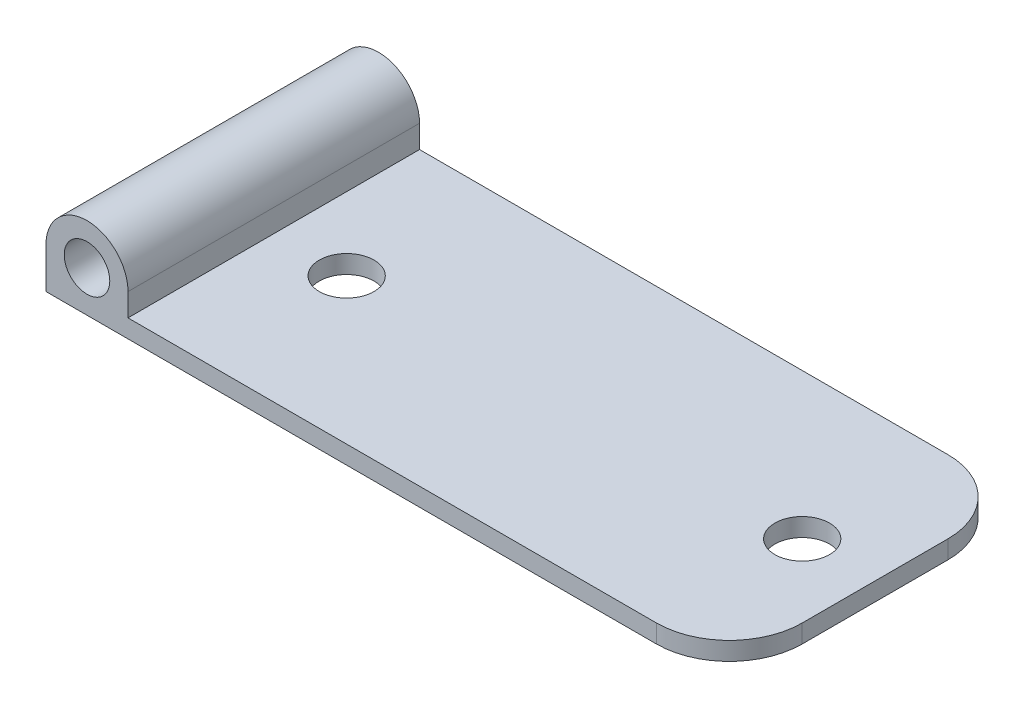
SolidWorks part; units mm, degrees
material "6061-T6 (SS)"
ref_plane "Front Plane" through (0, 0, 0) normal (0, 0, 1) x (1, 0, 0)
ref_plane "Top Plane" through (0, 0, 0) normal (0, 1, 0) x (1, 0, 0)
ref_plane "Right Plane" through (0, 0, 0) normal (1, 0, 0) x (0, 0, -1)
sketch "Sketch1" plane through (0, 0, 0) normal (0, 0, 1) x (1, 0, 0)
  line L0 (-3.9688, 0) -> (-3.9688, -3.9688)
  line L1 (3.9688, 0) -> (3.9688, -3.9688)
  line L2 (-3.9688, -3.9688) -> (-7.1437, -3.9688)
  line L3 (3.9688, -3.9688) -> (7.1438, -3.9688)
  line L4 (-7.1437, -3.9688) -> (-7.1437, -7.1438)
  line L5 (-7.1437, -7.1438) -> (7.1438, -7.1438)
  line L6 (-7.1437, 0) -> (-7.1437, -3.9688)
  line L7 (7.1437, 0) -> (7.1438, -3.9688)
  line L8 (7.1438, -3.9688) -> (111.9188, -3.9688)
  line L9 (111.9188, -3.9688) -> (111.9188, -7.1437)
  line L10 (7.1438, -7.1438) -> (7.1438, -3.9688)
  line L11 (-3.9688, -3.9688) -> (3.9688, -3.9688)
  line L12 (111.9188, -7.1437) -> (7.1438, -7.1438)
  circle A0 centre (0, 0) radius 3.9688
  arc A1 (-7.1437, 0) -> (7.1437, 0) centre (0, 0) cw
  dimension "D1" = 7.9375
  dimension "D6" = 3.175
  dimension "D2" = 104.775
  dimension "D3" = 3.175
  dimension "D7" = 3.175
  dimension "D8" = 3.175
extrude "Boss-Extrude1" add sketch "Sketch1" along normal blind 50.8
sketch "Sketch6" plane through (0, -3.9688, 0) normal (0, 1, 0) x (1, 0, 0)
  line L0 (111.9188, -25.4) -> (9.3644, -25.4) construction
  line L4 (7.1438, -50.8) -> (7.1438, 0) construction
  line L5 (111.9188, -50.8) -> (111.9188, 0) construction
  circle A0 centre (19.8438, -25.4) radius 4.7625
  circle A1 centre (99.2188, -25.4) radius 4.7625
  dimension "D1" = 9.525
  dimension "D2" = 9.525
  dimension "D3" = 12.7
  dimension "D4" = 12.7
extrude "Cut-Extrude3" cut sketch "Sketch6" against normal blind 12.7
fillet "Fillet2" radius 12.7 2 edges at (111.9188, -5.5562, 0) (111.9188, -5.5562, 50.8)
